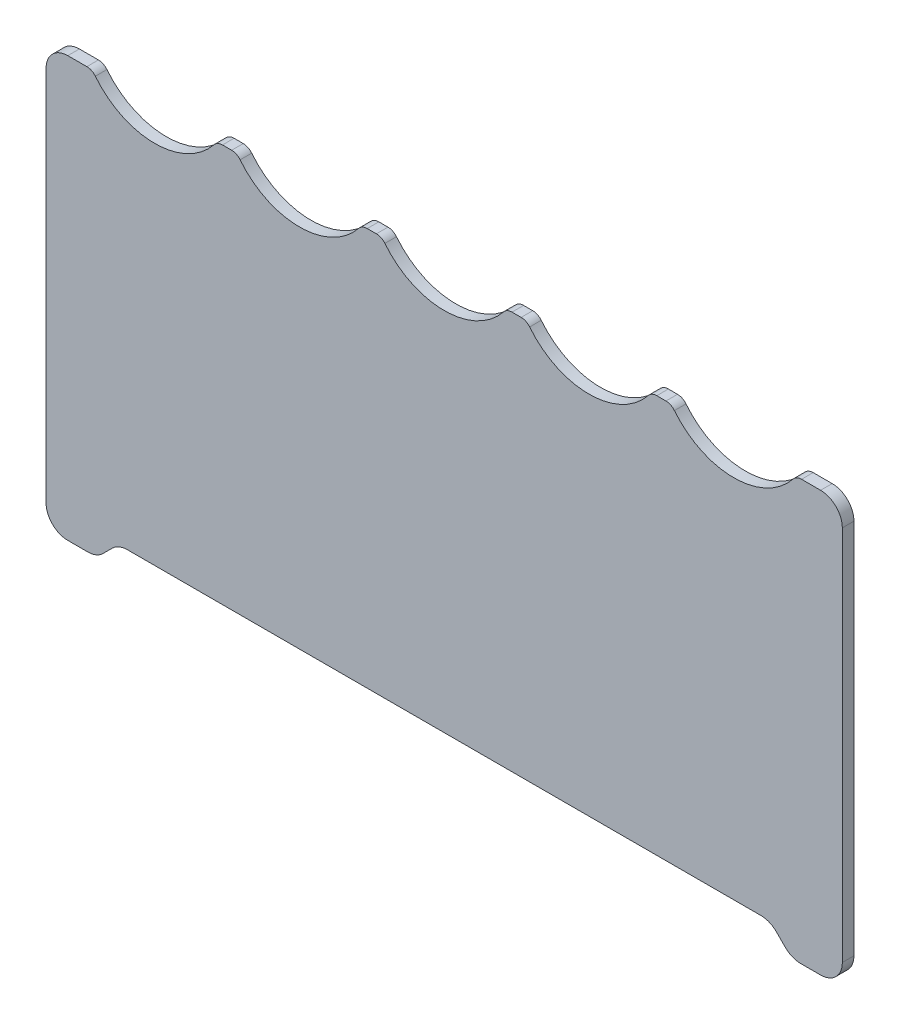
SolidWorks part; units mm, degrees
ref_plane "Front Plane" through (0, 0, 0) normal (0, 0, 1) x (1, 0, 0)
ref_plane "Top Plane" through (0, 0, 0) normal (0, 1, 0) x (1, 0, 0)
ref_plane "Right Plane" through (0, 0, 0) normal (1, 0, 0) x (0, 0, -1)
sketch "Sketch2" plane through (0, 0, 0) normal (0, 0, 1) x (1, 0, 0)
  line L0 (-47.1213, 0.8787) -> (-45.8787, 2.1213)
  line L2 (-55, 55) -> (-55, 3)
  line L3 (-52, 0) -> (-49.2426, 0)
  line L4 (55, 55) -> (55, 3)
  line L5 (-43.7574, 3) -> (43.7574, 3)
  line L6 (-10.6325, 58) -> (-9.3675, 58)
  line L7 (29.3675, 58) -> (30.6325, 58)
  line L9 (-30.6325, 58) -> (-29.3675, 58)
  line L10 (9.3675, 58) -> (10.6325, 58)
  line L11 (45.8787, 2.1213) -> (47.1213, 0.8787)
  line L12 (49.2426, 0) -> (52, 0)
  line L13 (-49.3675, 58) -> (-52, 58)
  line L14 (49.3675, 58) -> (52, 58)
  arc A2 (-48.1966, 57.4375) -> (-31.8034, 57.4375) centre (-40, 64) ccw
  arc A5 (31.8034, 57.4375) -> (48.1966, 57.4375) centre (40, 64) ccw
  arc A6 (11.8034, 57.4375) -> (28.1966, 57.4375) centre (20, 64) ccw
  arc A7 (-8.1966, 57.4375) -> (8.1966, 57.4375) centre (0, 64) ccw
  arc A8 (-30.6325, 58) -> (-31.8034, 57.4375) centre (-30.6325, 56.5) ccw
  arc A9 (-28.1966, 57.4375) -> (-11.8034, 57.4375) centre (-20, 64) ccw
  arc A10 (-29.3675, 58) -> (-28.1966, 57.4375) centre (-29.3675, 56.5) cw
  arc A11 (-11.8034, 57.4375) -> (-10.6325, 58) centre (-10.6325, 56.5) cw
  arc A12 (-9.3675, 58) -> (-8.1966, 57.4375) centre (-9.3675, 56.5) cw
  arc A13 (8.1966, 57.4375) -> (9.3675, 58) centre (9.3675, 56.5) cw
  arc A14 (10.6325, 58) -> (11.8034, 57.4375) centre (10.6325, 56.5) cw
  arc A15 (28.1966, 57.4375) -> (29.3675, 58) centre (29.3675, 56.5) cw
  arc A16 (31.8034, 57.4375) -> (30.6325, 58) centre (30.6325, 56.5) ccw
  arc A17 (49.3675, 58) -> (48.1966, 57.4375) centre (49.3675, 56.5) ccw
  arc A18 (-49.3675, 58) -> (-48.1966, 57.4375) centre (-49.3675, 56.5) cw
  arc A19 (52, 0) -> (55, 3) centre (52, 3) ccw
  arc A20 (47.1213, 0.8787) -> (49.2426, 0) centre (49.2426, 3) ccw
  arc A21 (43.7574, 3) -> (45.8787, 2.1213) centre (43.7574, 0) cw
  arc A22 (-45.8787, 2.1213) -> (-43.7574, 3) centre (-43.7574, 0) cw
  arc A23 (-47.1213, 0.8787) -> (-49.2426, 0) centre (-49.2426, 3) cw
  arc A24 (-55, 3) -> (-52, 0) centre (-52, 3) ccw
  arc A25 (-55, 55) -> (-52, 58) centre (-52, 55) cw
  arc A26 (55, 55) -> (52, 58) centre (52, 55) ccw
  point P25 (-11.3832, 58)
  point P32 (8.6168, 58)
  point P37 (28.6168, 58)
  point P40 (0, 3)
  point P52 (48, 0)
  point P55 (45, 3)
  point P58 (-45, 3)
  dimension "D3" = 1.5
  dimension "D5" = 10.5
  dimension "D14" = 1.5
  dimension "D15" = 3
  dimension "D2" = 58
  dimension "D4" = 110
  dimension "D7" = 6
  dimension "D6" = 20
  dimension "D8" = 20
  dimension "D9" = 20
  dimension "D10" = 20
  dimension "D11" = 135
  dimension "D12" = 3
  dimension "D13" = 90
extrude "Boss-Extrude1" add sketch "Sketch2" along normal blind 1.6
